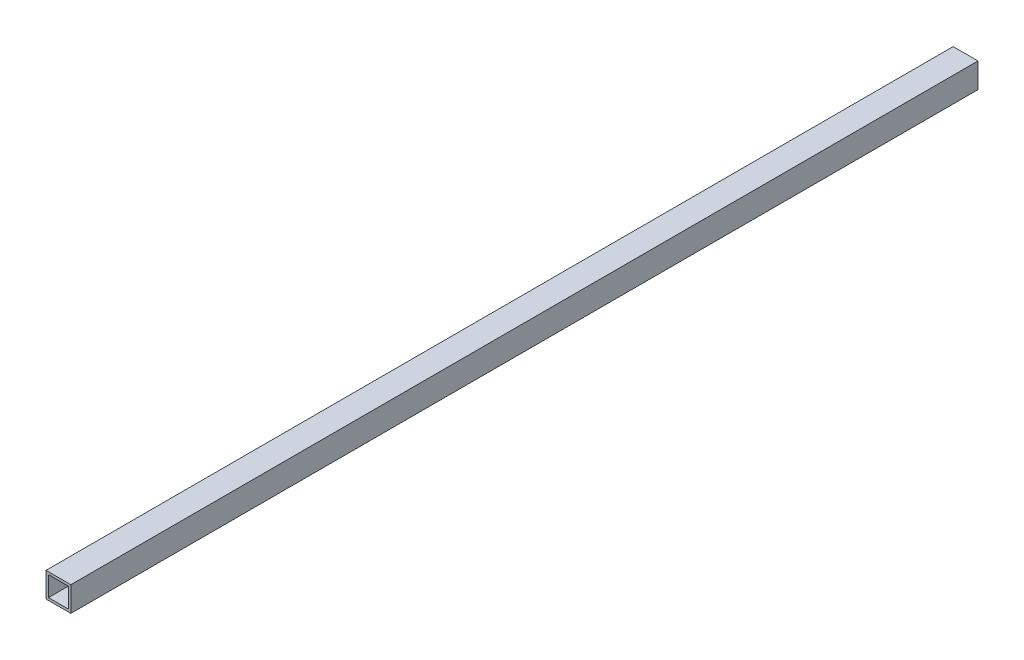
SolidWorks part; units mm, degrees
material "6061 Alloy"
ref_plane "Front Plane" through (0, 0, 0) normal (0, 0, 1) x (1, 0, 0)
ref_plane "Top Plane" through (0, 0, 0) normal (0, 1, 0) x (1, 0, 0)
ref_plane "Right Plane" through (0, 0, 0) normal (1, 0, 0) x (0, 0, -1)
sketch "Sketch1" plane through (0, 0, 0) normal (0, 0, 1) x (1, 0, 0)
  line L0 (-8, 8) -> (8, 8)
  line L1 (-10, -10) -> (10, -10)
  line L2 (-10, -10) -> (-10, 10)
  line L3 (-10, 10) -> (10, 10)
  line L4 (10, -10) -> (10, 10)
  line L5 (-10, -10) -> (10, 10) construction
  line L6 (-10, 10) -> (10, -10) construction
  line L7 (8, -8) -> (8, 8)
  line L8 (-8, -8) -> (8, -8)
  line L9 (-8, -8) -> (-8, 8)
  point P0 (0, 0)
  dimension "D1" = 20
  dimension "D2" = 20
  dimension "D3" = 2
extrude "Boss-Extrude1" add sketch "Sketch1" along normal blind 730
